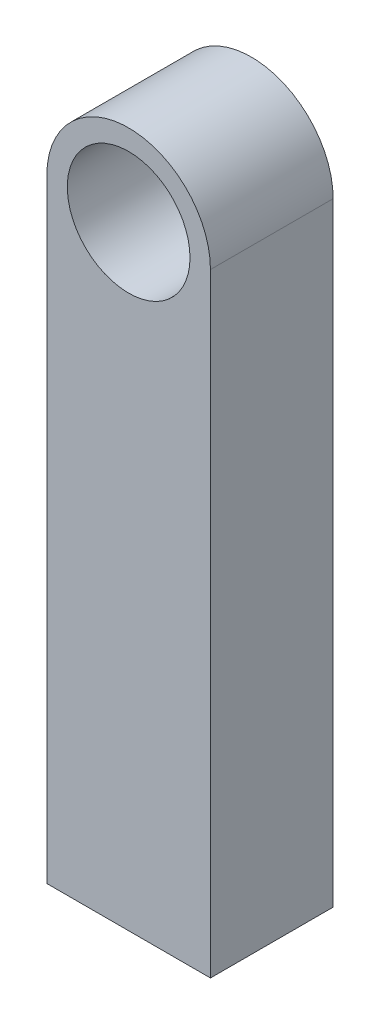
SolidWorks part; units mm, degrees
ref_plane "前视基准面" through (0, 0, 0) normal (0, 0, 1) x (1, 0, 0)
ref_plane "上视基准面" through (0, 0, 0) normal (0, 1, 0) x (1, 0, 0)
ref_plane "右视基准面" through (0, 0, 0) normal (1, 0, 0) x (0, 0, -1)
sketch "草图1" plane through (0, 0, 0) normal (0, 0, 1) x (1, 0, 0)
  line L0 (-2, 0) -> (-2, -15)
  line L1 (-2, -15) -> (2, -15)
  line L2 (2, 0) -> (2, -15)
  circle A0 centre (0, 0) radius 1.5
  circle A1 centre (0, 0) radius 2
  dimension "D1" = 3
  dimension "D2" = 4
  dimension "D3" = 15
extrude "凸台-拉伸1" add sketch "草图1" along normal blind 3 contours A1 L0 L1 L2 | A1 A0
sketch "草图2" plane through (0, -15, 0) normal (0, -1, 0) x (1, 0, 0)
  line L0 (-2, 3) -> (-2, 0) construction
  line L1 (-1.5, 0.5) -> (1.5, 0.5)
  line L2 (-1.5, 0.5) -> (-1.5, 2.5)
  line L3 (-1.5, 2.5) -> (1.5, 2.5)
  line L4 (1.5, 0.5) -> (1.5, 2.5)
  line L5 (2, 3) -> (2, 0) construction
  line L6 (-2, 3) -> (2, 3) construction
  line L7 (2.2, 0) -> (-2.2, 0) construction
  dimension "D1" = 0.5
  dimension "D2" = 0.5
  dimension "D3" = 0.5
  dimension "D4" = 0.5
extrude "切除-拉伸1" cut sketch "草图2" against normal blind 10
